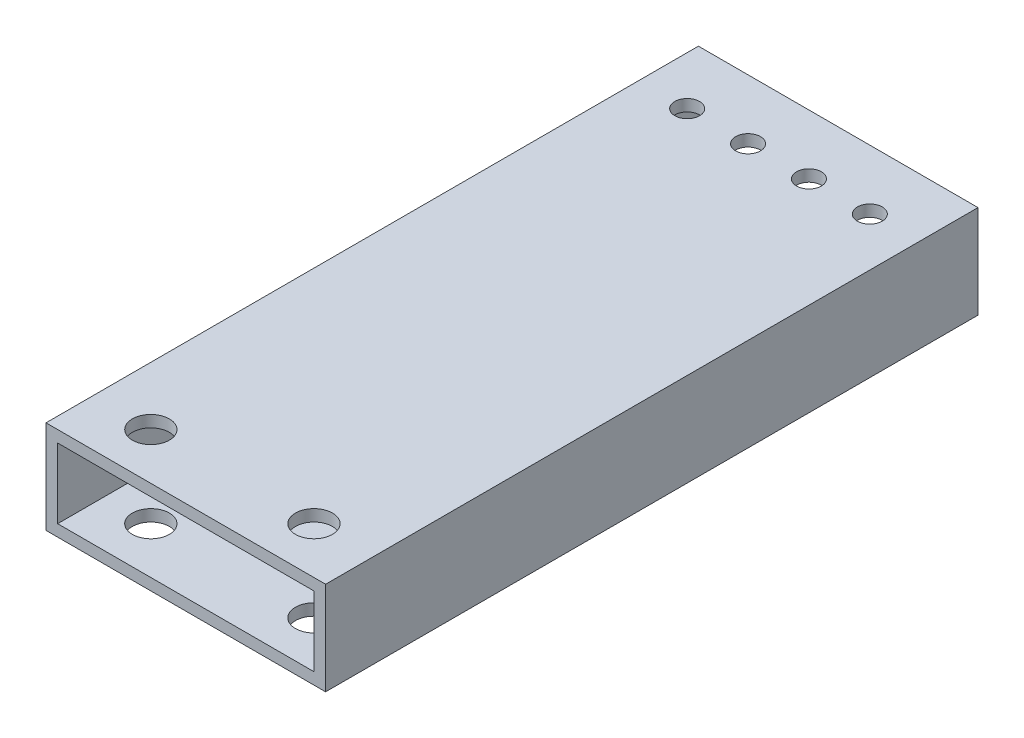
SolidWorks part; units mm, degrees
material "6061-T6 (SS)"
ref_plane "Front Plane" through (0, 0, 0) normal (0, 0, 1) x (1, 0, 0)
ref_plane "Top Plane" through (0, 0, 0) normal (0, 1, 0) x (1, 0, 0)
ref_plane "Right Plane" through (0, 0, 0) normal (1, 0, 0) x (0, 0, -1)
sketch "Sketch1" plane through (0, 0, 0) normal (0, 0, 1) x (1, 0, 0)
  line L0 (3.175, 3.175) -> (73.025, 3.175)
  line L1 (0, 0) -> (76.2, 0)
  line L2 (0, 0) -> (0, 25.4)
  line L3 (0, 25.4) -> (76.2, 25.4)
  line L4 (76.2, 0) -> (76.2, 25.4)
  line L5 (73.025, 3.175) -> (73.025, 22.225)
  line L6 (3.175, 22.225) -> (73.025, 22.225)
  line L7 (3.175, 3.175) -> (3.175, 22.225)
  dimension "D1" = 76.2
  dimension "D2" = 25.4
  dimension "D3" = 3.175
extrude "Boss-Extrude1" add sketch "Sketch1" along normal blind 177.8
sketch "Sketch2" plane through (0, 0, 0) normal (0, 0, -1) x (-1, 0, 0)
  line L0 (0, 0) -> (0, 127) construction
  line L1 (-76.2, 0) -> (-76.2, 127) construction
  dimension "D1" = 127
  dimension "D2" = 127
sketch "Sketch4" plane through (0, 25.4, 0) normal (0, 1, 0) x (1, 0, 0)
  circle A0 centre (13.2131, -16.2687) radius 3.3782
  circle A1 centre (29.8044, -16.2687) radius 3.3782
  circle A2 centre (46.3956, -16.2687) radius 3.3782
  circle A3 centre (62.9869, -16.2687) radius 3.3782
  dimension "D1" = 6.7564
  dimension "D2" = 6.7564
  dimension "D3" = 6.7564
  dimension "D4" = 6.7564
extrude "Cut-Extrude1" cut sketch "Sketch4" against normal through all
sketch "Sketch5" plane through (0, 0, 0) normal (0, -1, 0) x (1, 0, 0)
  line L0 (0, 177.8) -> (76.2, 177.8) construction
  line L4 (0, 177.8) -> (0, 0) construction
  circle A0 centre (60.325, 165.1) radius 5.0419
  circle A1 centre (15.875, 165.1) radius 5.0419
  dimension "D1" = 10.0838
  dimension "D2" = 10.0838
  dimension "D3" = 44.45
  dimension "D4" = 12.7
  dimension "D5" = 12.7
  dimension "D6" = 15.875
extrude "Cut-Extrude2" cut sketch "Sketch5" against normal through all
